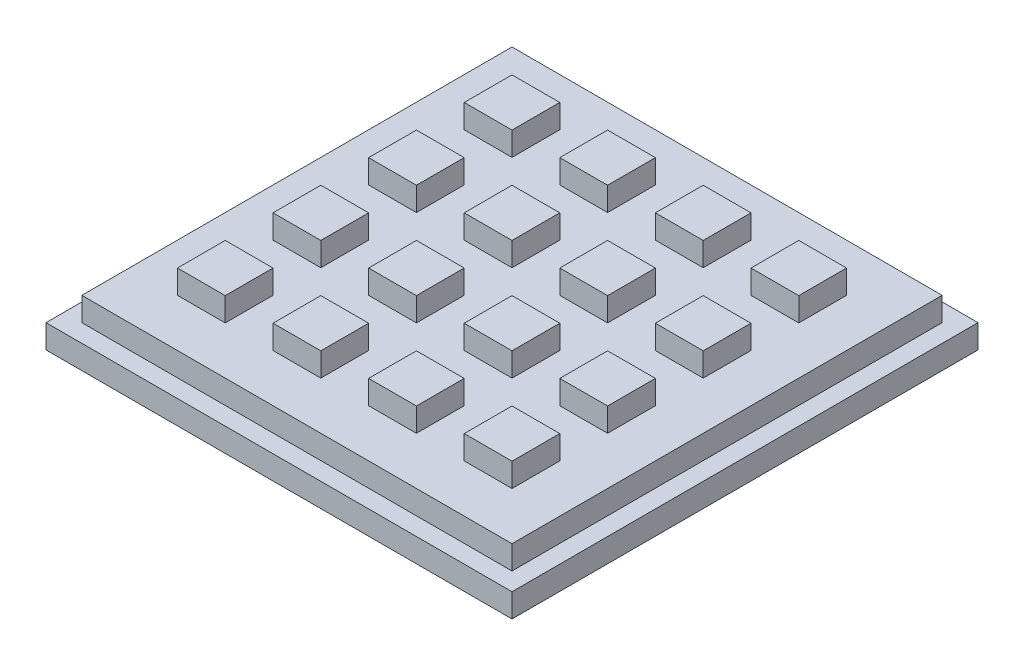
SolidWorks part; units mm, degrees
ref_plane "Front Plane" through (0, 0, 0) normal (0, 0, 1) x (1, 0, 0)
ref_plane "Top Plane" through (0, 0, 0) normal (0, 1, 0) x (1, 0, 0)
ref_plane "Right Plane" through (0, 0, 0) normal (1, 0, 0) x (0, 0, -1)
sketch "Sketch1" plane through (0, 0, 0) normal (0, 1, 0) x (1, 0, 0)
  line L1 (0, 0) -> (65, 0)
  line L2 (0, 0) -> (0, 65)
  line L3 (0, 65) -> (65, 65)
  line L4 (65, 0) -> (65, 65)
  dimension "D1" = 65
extrude "Boss-Extrude1" add sketch "Sketch1" along normal blind 3.3
sketch "Sketch2" plane through (0, 3.3, 0) normal (0, 1, 0) x (1, 0, 0)
  line L1 (2.5, 2.5) -> (62.5, 2.5)
  line L2 (2.5, 2.5) -> (2.5, 62.5)
  line L3 (2.5, 62.5) -> (62.5, 62.5)
  line L4 (62.5, 2.5) -> (62.5, 62.5)
  line L5 (65, 65) -> (62.5, 65) construction
  line L6 (65, 65) -> (65, 62.5) construction
  line L7 (65, 62.5) -> (62.5, 62.5) construction
  line L8 (62.5, 65) -> (62.5, 62.5) construction
  line L9 (2.5, 2.5) -> (0, 2.5) construction
  line L10 (2.5, 2.5) -> (2.5, 0) construction
  line L11 (2.5, 0) -> (0, 0) construction
  line L12 (0, 2.5) -> (0, 0) construction
  dimension "D1" = 2.5
extrude "Boss-Extrude2" add sketch "Sketch2" along normal blind 3.3
sketch "Sketch3" plane through (0, 6.6, 0) normal (0, 1, 0) x (1, 0, 0)
  line L0 (15.8333, 55.8333) -> (22.5, 55.8333) construction
  line L1 (2.5, 62.5) -> (9.1667, 62.5) construction
  line L2 (2.5, 62.5) -> (2.5, 55.8333) construction
  line L3 (2.5, 55.8333) -> (9.1667, 55.8333) construction
  line L4 (9.1667, 62.5) -> (9.1667, 55.8333) construction
  line L5 (9.1667, 55.8333) -> (15.8333, 55.8333)
  line L6 (9.1667, 55.8333) -> (9.1667, 49.1667)
  line L7 (9.1667, 49.1667) -> (15.8333, 49.1667)
  line L8 (15.8333, 55.8333) -> (15.8333, 49.1667)
  line L9 (22.5, 55.8333) -> (29.1667, 55.8333)
  line L10 (22.5, 55.8333) -> (22.5, 49.1667)
  line L11 (22.5, 49.1667) -> (29.1667, 49.1667)
  line L12 (29.1667, 55.8333) -> (29.1667, 49.1667)
  line L13 (35.8333, 55.8333) -> (42.5, 55.8333)
  line L14 (35.8333, 55.8333) -> (35.8333, 49.1667)
  line L15 (35.8333, 49.1667) -> (42.5, 49.1667)
  line L16 (42.5, 55.8333) -> (42.5, 49.1667)
  line L17 (49.1667, 55.8333) -> (55.8333, 55.8333)
  line L18 (49.1667, 55.8333) -> (49.1667, 49.1667)
  line L19 (49.1667, 49.1667) -> (55.8333, 49.1667)
  line L20 (55.8333, 55.8333) -> (55.8333, 49.1667)
  line L21 (29.1667, 55.8333) -> (35.8333, 55.8333) construction
  line L22 (42.5, 55.8333) -> (49.1667, 55.8333) construction
  line L23 (55.8333, 55.8333) -> (62.5, 55.8333) construction
  line L24 (62.5, 2.5) -> (62.5, 62.5) construction
  line L25 (2.5, 62.5) -> (2.5, 2.5) construction
  line L26 (9.1667, 49.1667) -> (62.5, 49.1667) construction
  line L30 (55.8333, 49.1667) -> (2.5, 49.1667) construction
  line L34 (9.1667, 49.1667) -> (15.8333, 49.1667) construction
extrude "Boss-Extrude3" add sketch "Sketch3" along normal blind 3.3
pattern_linear "LPattern1" count 4 spacing 13.3333 along (0, 0, 1) of "Boss-Extrude3"
